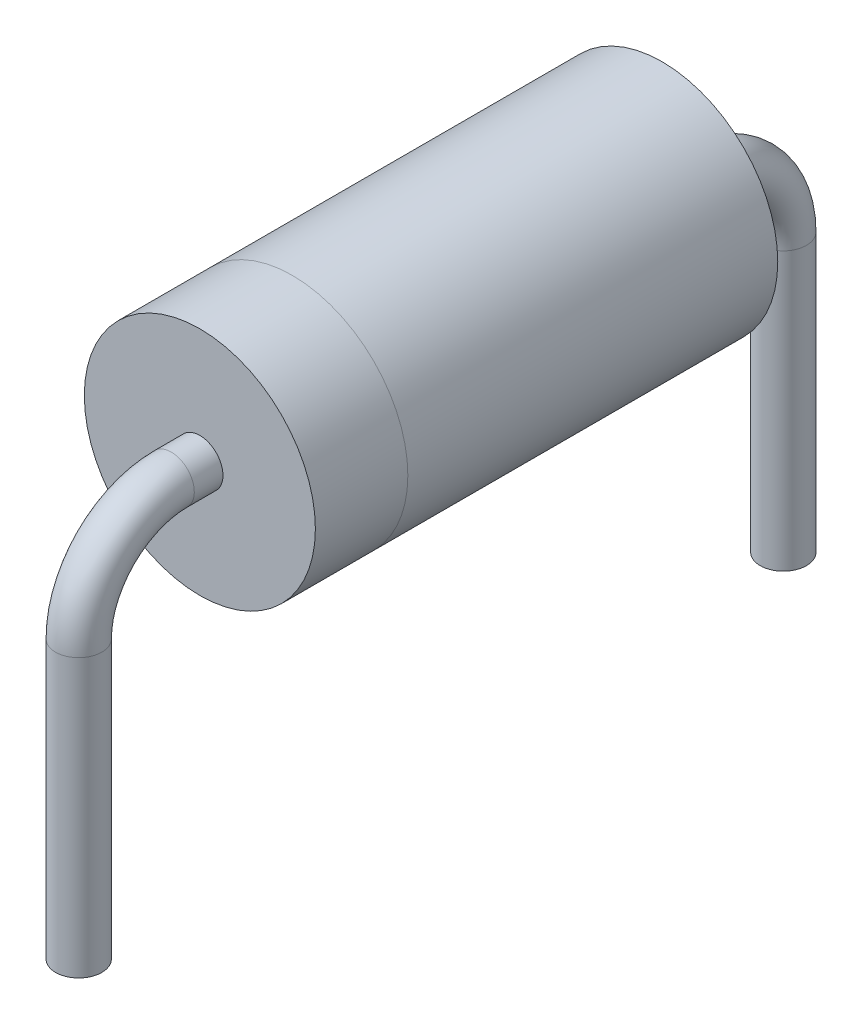
SolidWorks part; units mm, degrees
ref_plane "Plan de face" through (0, 0, 0) normal (0, 0, 1) x (1, 0, 0)
ref_plane "Plan de dessus" through (0, 0, 0) normal (0, 1, 0) x (1, 0, 0)
ref_plane "Plan de droite" through (0, 0, 0) normal (1, 0, 0) x (0, 0, -1)
sketch "Esquisse1" plane through (0, 0, 0) normal (0, 0, 1) x (1, 0, 0)
  circle A0 centre (0, 0) radius 1.25
  dimension "D1" = 2.5
extrude "Boss.-Extru.1" add sketch "Esquisse1" along normal blind 4
sketch "Esquisse2" plane through (0, 0, 4) normal (0, 0, 1) x (1, 0, 0)
  circle A0 centre (0, 0) radius 1.2495
  dimension "D1" = 2.499
extrude "Boss.-Extru.2" add sketch "Esquisse2" along normal blind 1
ref_plane "Plan1" through (0, 0, 5) normal (0, 0, 1) x (1, 0, 0)
sketch "Esquisse3" plane through (0, 0, 0) normal (1, 0, 0) x (0, 0, -1)
  line L0 (-5, 0) -> (-5.31, 0)
  line L1 (-5, 1.3744) -> (-5, -1.3744) construction
  line L2 (-6.31, -1) -> (-6.31, -4)
  arc A0 (-5.31, 0) -> (-6.31, -1) centre (-5.31, -1) ccw
  point P8 (-6.31, 0)
  dimension "D3" = 1
  dimension "D1" = 1.31
  dimension "D2" = 4
sketch "Esquisse4" plane through (0, 0, 5) normal (0, 0, 1) x (1, 0, 0)
  circle A0 centre (0, 0) radius 0.25
  dimension "D1" = 0.5
sweep "Balayage1" add profiles "Esquisse4" path "Esquisse3"
ref_plane "Plan2" through (0, 0, 2.5) normal (0, 0, 1) x (1, 0, 0)
mirror "Symétrie1" about plane through (0, 0, 2.5) normal (0, 0, 1) of "Balayage1"
